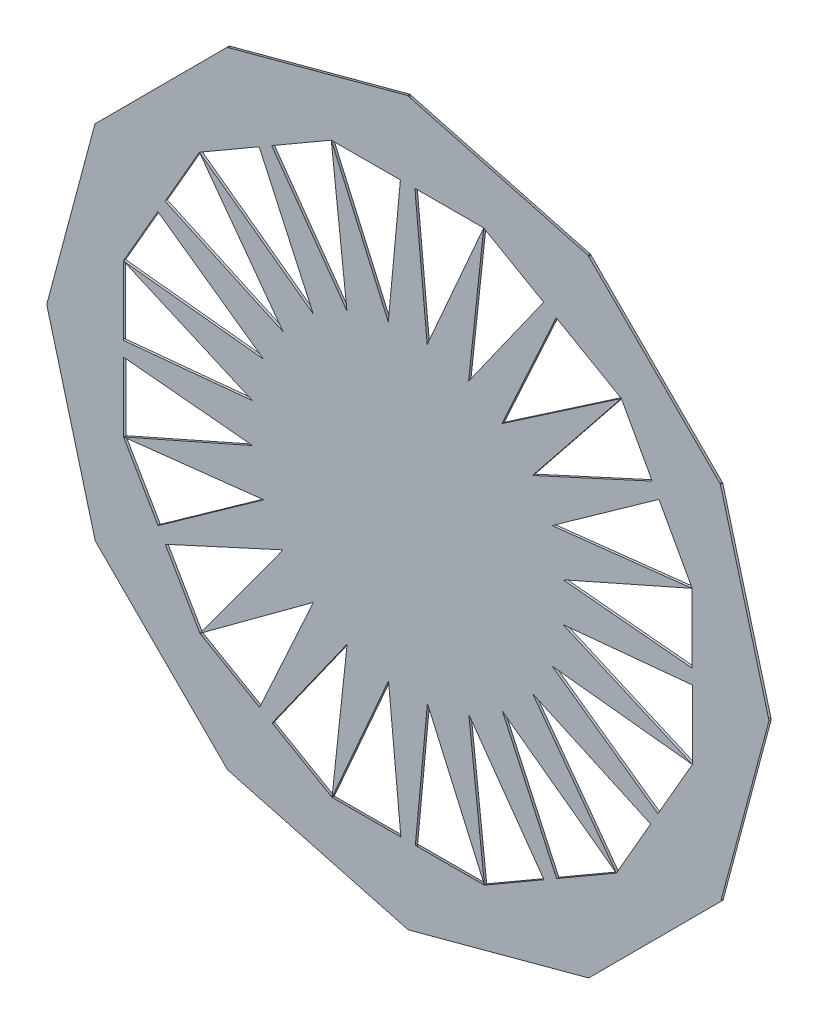
SolidWorks part; units mm, degrees
ref_plane "Alzado" through (0, 0, 0) normal (0, 0, 1) x (1, 0, 0)
ref_plane "Planta" through (0, 0, 0) normal (0, 1, 0) x (1, 0, 0)
ref_plane "Vista lateral" through (0, 0, 0) normal (1, 0, 0) x (0, 0, -1)
sketch "Model" plane through (0, 0, 0) normal (0, 0, 1) x (1, 0, 0)
  line L0 (38.9349, 3.8097) -> (36.4342, 9.4647)
  line L1 (36.4342, 9.4647) -> (35.5912, 0.4417)
  line L2 (35.5912, 0.4417) -> (34.73, 9.4635)
  line L3 (34.73, 9.4635) -> (32.253, 3.8008)
  line L4 (32.253, 3.8008) -> (32.9149, 9.9485)
  line L5 (32.9149, 9.9485) -> (27.6733, 2.5559)
  line L6 (27.6733, 2.5559) -> (31.4384, 10.7996)
  line L7 (31.4384, 10.7996) -> (26.4619, 7.134)
  line L8 (26.4619, 7.134) -> (30.1089, 12.1272)
  line L9 (30.1089, 12.1272) -> (21.8733, 8.3457)
  line L10 (21.8733, 8.3457) -> (29.2558, 13.6025)
  line L11 (29.2558, 13.6025) -> (23.1133, 12.9163)
  line L12 (23.1133, 12.9163) -> (28.7683, 15.4169)
  line L13 (28.7683, 15.4169) -> (19.7453, 16.2599)
  line L14 (19.7453, 16.2599) -> (28.7671, 17.1212)
  line L15 (28.7671, 17.1212) -> (23.1044, 19.5981)
  line L16 (23.1044, 19.5981) -> (29.2521, 18.9363)
  line L17 (29.2521, 18.9363) -> (21.8595, 24.1778)
  line L18 (21.8595, 24.1778) -> (30.1032, 20.4128)
  line L19 (30.1032, 20.4128) -> (26.4376, 25.3892)
  line L20 (26.4376, 25.3892) -> (31.4308, 21.7422)
  line L21 (31.4308, 21.7422) -> (27.6493, 29.9778)
  line L22 (27.6493, 29.9778) -> (32.9061, 22.5953)
  line L23 (32.9061, 22.5953) -> (32.2199, 28.7378)
  line L24 (32.2199, 28.7378) -> (34.7205, 23.0829)
  line L25 (34.7205, 23.0829) -> (35.5635, 32.1058)
  line L26 (35.5635, 32.1058) -> (36.4248, 23.084)
  line L27 (36.4248, 23.084) -> (38.9017, 28.7467)
  line L28 (38.9017, 28.7467) -> (38.2399, 22.599)
  line L29 (38.2399, 22.599) -> (43.4814, 29.9916)
  line L30 (43.4814, 29.9916) -> (39.7019, 21.7163)
  line L31 (39.7019, 21.7163) -> (44.938, 25.2901)
  line L32 (44.938, 25.2901) -> (41.0458, 20.4204)
  line L33 (41.0458, 20.4204) -> (49.2814, 24.2018)
  line L34 (49.2814, 24.2018) -> (41.8989, 18.945)
  line L35 (41.8989, 18.945) -> (48.0414, 19.6313)
  line L36 (48.0414, 19.6313) -> (42.3865, 17.1306)
  line L37 (42.3865, 17.1306) -> (51.4094, 16.2876)
  line L38 (51.4094, 16.2876) -> (42.3876, 15.4264)
  line L39 (42.3876, 15.4264) -> (48.0503, 12.9494)
  line L40 (48.0503, 12.9494) -> (41.9026, 13.6113)
  line L41 (41.9026, 13.6113) -> (49.2952, 8.3697)
  line L42 (49.2952, 8.3697) -> (41.0515, 12.1348)
  line L43 (41.0515, 12.1348) -> (44.7171, 7.1583)
  line L44 (44.7171, 7.1583) -> (39.724, 10.8053)
  line L45 (39.724, 10.8053) -> (43.5054, 2.5697)
  line L46 (43.5054, 2.5697) -> (38.2486, 9.9522)
  line L47 (38.2486, 9.9522) -> (38.9349, 3.8097)
extrude "Saliente-Extruir1" add sketch "Model" along normal blind 0.1
